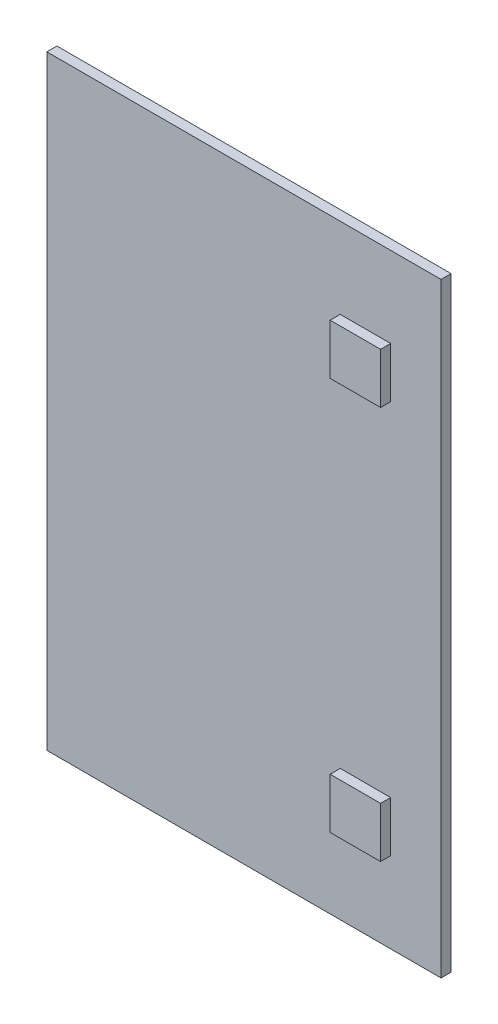
SolidWorks part; units mm, degrees
ref_plane "Plan de face" through (0, 0, 0) normal (0, 0, 1) x (1, 0, 0)
ref_plane "Plan de dessus" through (0, 0, 0) normal (0, 1, 0) x (1, 0, 0)
ref_plane "Plan de droite" through (0, 0, 0) normal (1, 0, 0) x (0, 0, -1)
sketch "Esquisse1" plane through (0, 0, 0) normal (0, 0, 1) x (1, 0, 0)
  line L2 (-18.5941, -0.4534) -> (-409.5941, -0.4534)
  line L3 (-18.5941, -0.4534) -> (-18.5941, 599.5466)
  line L4 (-18.5941, 599.5466) -> (-409.5941, 599.5466)
  line L5 (-409.5941, -0.4534) -> (-409.5941, 599.5466)
  dimension "D1" = 391
  dimension "D2" = 600
extrude "Boss.-Extru.1" add sketch "Esquisse1" against normal blind 10
sketch "Esquisse2" plane through (0, 0, 0) normal (0, 0, 1) x (1, 0, 0)
  line L0 (-18.5941, 599.5466) -> (-409.5941, 599.5466) construction
  line L1 (-118.5941, 519.5466) -> (-68.5941, 519.5466)
  line L2 (-118.5941, 519.5466) -> (-118.5941, 469.5466)
  line L3 (-118.5941, 469.5466) -> (-68.5941, 469.5466)
  line L4 (-68.5941, 519.5466) -> (-68.5941, 469.5466)
  line L5 (-118.5941, 129.5466) -> (-68.5941, 129.5466)
  line L6 (-118.5941, 129.5466) -> (-118.5941, 79.5466)
  line L7 (-118.5941, 79.5466) -> (-68.5941, 79.5466)
  line L8 (-68.5941, 129.5466) -> (-68.5941, 79.5466)
  line L9 (-409.5941, -0.4534) -> (-18.5941, -0.4534) construction
  line L10 (-18.5941, -0.4534) -> (-18.5941, 599.5466) construction
  dimension "D1" = 50
  dimension "D2" = 50
  dimension "D3" = 50
  dimension "D4" = 50
  dimension "D5" = 80
  dimension "D6" = 80
  dimension "D7" = 50
extrude "Boss.-Extru.2" add sketch "Esquisse2" along normal blind 10
